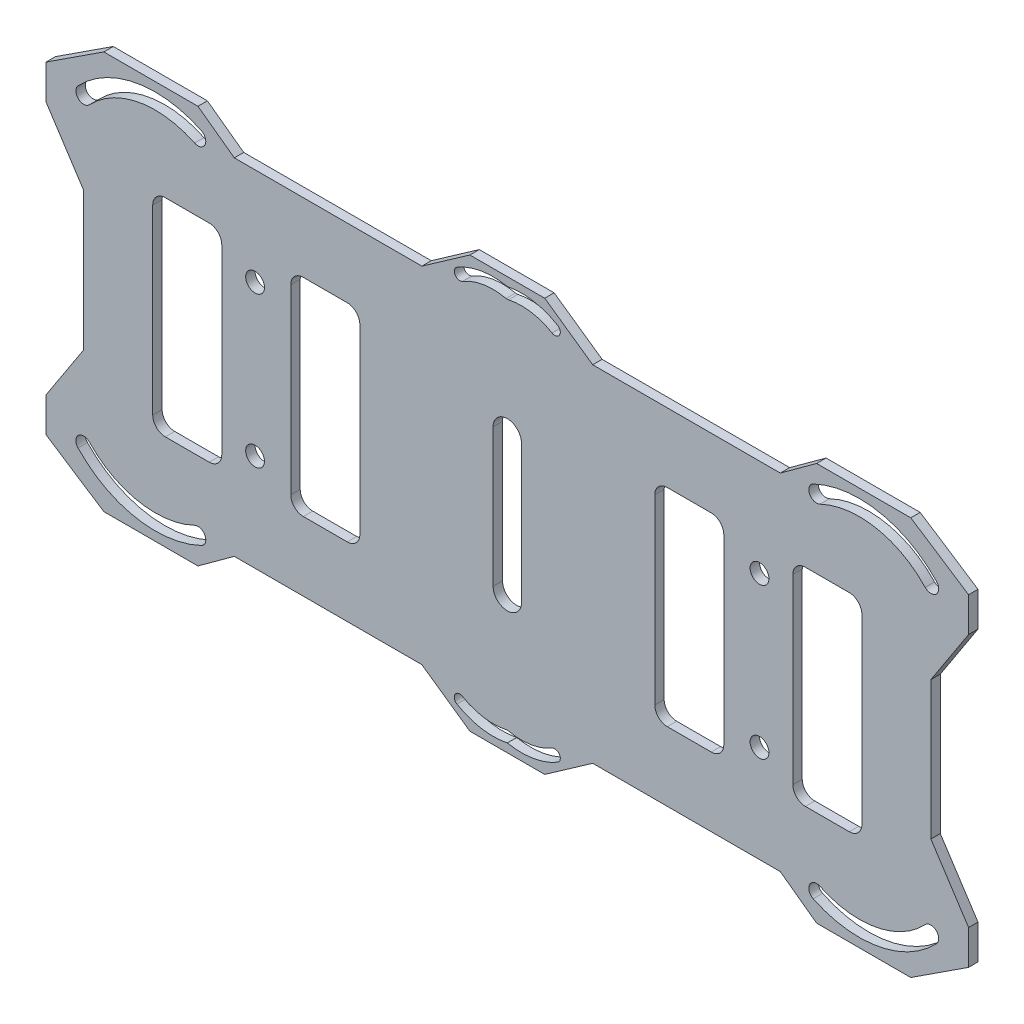
SolidWorks part; units mm, degrees
ref_plane "Piano frontale" through (0, 0, 0) normal (0, 0, 1) x (1, 0, 0)
ref_plane "Piano superiore" through (0, 0, 0) normal (0, 1, 0) x (1, 0, 0)
ref_plane "Piano destro" through (0, 0, 0) normal (1, 0, 0) x (0, 0, -1)
sketch "Schizzo1" plane through (0, 0, 0) normal (0, 0, 1) x (1, 0, 0)
  line L0 (-13.6152, -27.5) -> (-5.9645, -32.8595)
  line L1 (13.6152, -27.5) -> (43.5, -27.5)
  line L2 (-67.5, -11) -> (-67.5, 11)
  line L5 (-67.5, -27.5) -> (67.5, 27.5) construction
  line L6 (-67.5, 27.5) -> (67.5, -27.5) construction
  line L7 (55, 0) -> (-55, 0) construction
  line L8 (-54.5, -16.5) -> (-47.5, -16.5)
  line L9 (-56.5, -14.5) -> (-56.5, 14.5)
  line L11 (-45.5, -14.5) -> (-45.5, 14.5)
  line L12 (-56.5, -16.5) -> (-45.5, 16.5) construction
  line L13 (-56.5, 16.5) -> (-45.5, -16.5) construction
  line L14 (-67.5, -11) -> (-73.5081, -20.2143)
  line L15 (-32.5, -16.5) -> (-25.5, -16.5)
  line L16 (-34.5, -14.5) -> (-34.5, 14.5)
  line L18 (-23.5, -14.5) -> (-23.5, 14.5)
  line L19 (-34.5, -16.5) -> (-23.5, 16.5) construction
  line L20 (-34.5, 16.5) -> (-23.5, -16.5) construction
  line L21 (-73.5081, -20.2143) -> (-73.5081, -25.7143)
  line L22 (-73.5081, -25.7143) -> (-64.2938, -31.7224)
  line L23 (-64.2938, -31.7224) -> (-49.2938, -31.7224)
  line L24 (-49.2938, -31.7224) -> (-43.5, -27.5)
  line L25 (-5.9645, -32.8595) -> (5.9645, -32.8595)
  line L26 (0, -55) -> (0, 55) construction
  line L27 (13.6152, -27.5) -> (5.9645, -32.8595)
  line L29 (45.5, -14.5) -> (45.5, 14.5)
  line L30 (54.5, -16.5) -> (47.5, -16.5)
  line L31 (56.5, -14.5) -> (56.5, 14.5)
  line L33 (23.5, -14.5) -> (23.5, 14.5)
  line L34 (32.5, -16.5) -> (25.5, -16.5)
  line L35 (34.5, -14.5) -> (34.5, 14.5)
  line L36 (49.2938, -31.7224) -> (43.5, -27.5)
  line L37 (64.2938, -31.7224) -> (49.2938, -31.7224)
  line L38 (73.5081, -25.7143) -> (64.2938, -31.7224)
  line L39 (73.5081, -20.2143) -> (73.5081, -25.7143)
  line L40 (67.5, -11) -> (73.5081, -20.2143)
  line L41 (67.5, -11) -> (67.5, 11)
  line L42 (-13.6152, 27.5) -> (-43.5, 27.5)
  line L43 (43.5, -27.5) -> (13.6152, -27.5)
  line L44 (67.5, -11) -> (67.5, 11)
  line L45 (43.5, 27.5) -> (13.6152, 27.5)
  line L46 (-13.6152, -27.5) -> (-43.5, -27.5)
  line L47 (-67.5, -11) -> (-67.5, 11)
  line L48 (67.5, 11) -> (73.5081, 20.2143)
  line L49 (73.5081, 20.2143) -> (73.5081, 25.7143)
  line L50 (73.5081, 25.7143) -> (64.2938, 31.7224)
  line L51 (64.2938, 31.7224) -> (49.2938, 31.7224)
  line L52 (49.2938, 31.7224) -> (43.5, 27.5)
  line L53 (32.5, 16.5) -> (25.5, 16.5)
  line L54 (54.5, 16.5) -> (47.5, 16.5)
  line L55 (13.6152, 27.5) -> (5.9645, 32.8595)
  line L56 (-5.9645, 32.8595) -> (5.9645, 32.8595)
  line L57 (-49.2938, 31.7224) -> (-43.5, 27.5)
  line L58 (-64.2938, 31.7224) -> (-49.2938, 31.7224)
  line L59 (-73.5081, 25.7143) -> (-64.2938, 31.7224)
  line L60 (-73.5081, 20.2143) -> (-73.5081, 25.7143)
  line L61 (-32.5, 16.5) -> (-25.5, 16.5)
  line L62 (-67.5, 11) -> (-73.5081, 20.2143)
  line L63 (-54.5, 16.5) -> (-47.5, 16.5)
  line L64 (13.6152, 27.5) -> (43.5, 27.5)
  line L65 (-13.6152, 27.5) -> (-5.9645, 32.8595)
  line L66 (-67.5, 25.4461) -> (-67.5, 25.8768)
  line L67 (-67.5, 25.4461) -> (-67.5, 25.8768)
  line L68 (0, 11) -> (0, -11) construction
  line L69 (2.2614, 11) -> (2.2614, -11)
  line L70 (-2.2614, 11) -> (-2.2614, -11)
  arc A0 (-25.5, -16.5) -> (-23.5, -14.5) centre (-25.5, -14.5) ccw
  arc A1 (-32.5, -16.5) -> (-34.5, -14.5) centre (-32.5, -14.5) cw
  arc A6 (-47.5, -16.5) -> (-45.5, -14.5) centre (-47.5, -14.5) ccw
  arc A7 (-54.5, -16.5) -> (-56.5, -14.5) centre (-54.5, -14.5) cw
  arc A8 (-67.5, -24.1318) -> (-49.2938, -27.5) centre (-56.089, -13.341) ccw construction
  arc A9 (-68.4056, -24.9882) -> (-48.7545, -28.6237) centre (-56.089, -13.341) ccw
  arc A10 (-66.5944, -23.2754) -> (-49.8331, -26.3763) centre (-56.089, -13.341) ccw
  arc A11 (-66.5944, -23.2754) -> (-68.4056, -24.9882) centre (-67.5, -24.1318) ccw
  arc A12 (-48.7545, -28.6237) -> (-49.8331, -26.3763) centre (-49.2938, -27.5) ccw
  circle A13 centre (-40.1914, -12) radius 1.5
  circle A14 centre (40.1914, 12) radius 1.5
  arc A15 (-8.0181, -30.1482) -> (0.1871, -31.4567) centre (-2.2501, -20.359) ccw
  arc A16 (-7.1323, -28.6449) -> (-0.1871, -29.7524) centre (-2.2501, -20.359) ccw
  arc A17 (-7.1323, -28.6449) -> (-8.0181, -30.1482) centre (-7.5752, -29.3966) ccw
  arc A18 (0.1871, -29.7524) -> (-0.1871, -29.7524) centre (0, -30.6046) ccw
  circle A19 centre (40.1914, -12) radius 1.5
  arc A20 (8.0181, -30.1482) -> (-0.1871, -31.4567) centre (2.2501, -20.359) cw
  arc A21 (7.1323, -28.6449) -> (0.1871, -29.7524) centre (2.2501, -20.359) cw
  arc A22 (7.1323, -28.6449) -> (8.0181, -30.1482) centre (7.5752, -29.3966) cw
  arc A23 (-0.1871, -29.7524) -> (0.1871, -29.7524) centre (0, -30.6046) cw
  arc A25 (47.5, -16.5) -> (45.5, -14.5) centre (47.5, -14.5) cw
  arc A27 (54.5, -16.5) -> (56.5, -14.5) centre (54.5, -14.5) ccw
  arc A29 (25.5, -16.5) -> (23.5, -14.5) centre (25.5, -14.5) cw
  arc A30 (32.5, -16.5) -> (34.5, -14.5) centre (32.5, -14.5) ccw
  arc A32 (67.5, -24.1318) -> (49.2938, -27.5) centre (56.089, -13.341) cw construction
  arc A33 (68.4056, -24.9882) -> (48.7545, -28.6237) centre (56.089, -13.341) cw
  arc A34 (66.5944, -23.2754) -> (49.8331, -26.3763) centre (56.089, -13.341) cw
  arc A35 (66.5944, -23.2754) -> (68.4056, -24.9882) centre (67.5, -24.1318) cw
  arc A36 (48.7545, -28.6237) -> (49.8331, -26.3763) centre (49.2938, -27.5) cw
  arc A37 (-67.5, 24.1318) -> (-49.2938, 27.5) centre (-56.089, 13.341) cw construction
  arc A38 (-68.4056, 24.9882) -> (-48.7545, 28.6237) centre (-56.089, 13.341) cw
  arc A39 (-66.5944, 23.2754) -> (-49.8331, 26.3763) centre (-56.089, 13.341) cw
  arc A40 (-66.5944, 23.2754) -> (-68.4056, 24.9882) centre (-67.5, 24.1318) cw
  arc A41 (-48.7545, 28.6237) -> (-49.8331, 26.3763) centre (-49.2938, 27.5) cw
  arc A42 (67.5, 24.1318) -> (49.2938, 27.5) centre (56.089, 13.341) ccw construction
  arc A43 (68.4056, 24.9882) -> (48.7545, 28.6237) centre (56.089, 13.341) ccw
  arc A44 (66.5944, 23.2754) -> (49.8331, 26.3763) centre (56.089, 13.341) ccw
  arc A45 (66.5944, 23.2754) -> (68.4056, 24.9882) centre (67.5, 24.1318) ccw
  arc A46 (48.7545, 28.6237) -> (49.8331, 26.3763) centre (49.2938, 27.5) ccw
  arc A47 (2.2614, 11) -> (-2.2614, 11) centre (0, 11) ccw
  arc A48 (-2.2614, -11) -> (2.2614, -11) centre (0, -11) ccw
  arc A49 (32.5, 16.5) -> (34.5, 14.5) centre (32.5, 14.5) cw
  arc A50 (25.5, 16.5) -> (23.5, 14.5) centre (25.5, 14.5) ccw
  arc A51 (54.5, 16.5) -> (56.5, 14.5) centre (54.5, 14.5) cw
  arc A52 (47.5, 16.5) -> (45.5, 14.5) centre (47.5, 14.5) ccw
  arc A53 (-0.1871, 29.7524) -> (0.1871, 29.7524) centre (0, 30.6046) ccw
  arc A54 (7.1323, 28.6449) -> (8.0181, 30.1482) centre (7.5752, 29.3966) ccw
  arc A55 (7.1323, 28.6449) -> (0.1871, 29.7524) centre (2.2501, 20.359) ccw
  arc A56 (8.0181, 30.1482) -> (-0.1871, 31.4567) centre (2.2501, 20.359) ccw
  arc A57 (0.1871, 29.7524) -> (-0.1871, 29.7524) centre (0, 30.6046) cw
  arc A58 (-7.1323, 28.6449) -> (-8.0181, 30.1482) centre (-7.5752, 29.3966) cw
  arc A59 (-7.1323, 28.6449) -> (-0.1871, 29.7524) centre (-2.2501, 20.359) cw
  arc A60 (-8.0181, 30.1482) -> (0.1871, 31.4567) centre (-2.2501, 20.359) cw
  circle A61 centre (-40.1914, 12) radius 1.5
  arc A62 (-54.5, 16.5) -> (-56.5, 14.5) centre (-54.5, 14.5) ccw
  arc A63 (-47.5, 16.5) -> (-45.5, 14.5) centre (-47.5, 14.5) cw
  arc A64 (-32.5, 16.5) -> (-34.5, 14.5) centre (-32.5, 14.5) ccw
  arc A65 (-25.5, 16.5) -> (-23.5, 14.5) centre (-25.5, 14.5) cw
  point P0 (0, 0)
  point P6 (-51, 0)
  point P13 (-29, 0)
  point P29 (-58.946, 28.7841)
  point P51 (-58.946, -28.7841)
  point P66 (-3.902, -30.7178)
  point P72 (0, -32.8595)
  point P76 (3.902, -30.7178)
  point P89 (58.946, 28.7841)
  point P108 (58.946, -28.7841)
  point P166 (3.902, 30.7178)
  point P167 (0, 32.8595)
  point P168 (-3.902, 30.7178)
  point P176 (0, 0)
  dimension "D8" = 2
  dimension "D15" = 3
  dimension "D1" = 135
  dimension "D2" = 55
  dimension "D3" = 16.5
  dimension "D4" = 11
  dimension "D5" = 38.5
  dimension "D6" = 11
  dimension "D7" = 33
  dimension "D9" = 11
  dimension "D10" = 11
  dimension "D11" = 5.5
  dimension "D12" = 11
  dimension "D13" = 15
  dimension "D14" = 24
  dimension "D16" = 12
extrude "Estrusione-Estrusione1" add sketch "Schizzo1" along normal mid plane 1.5 contours L65 L42 L57 L58 L59 L60 L62 L2 L14 L21 L22 L23 L24 L46 L0 L25 L27 L1 L36 L37 L38 L39 L40 L41 L48 L49 L50 L51 L52 L45 L55 L56 A58 A60 A56 A54 A55 A53 A59 A38 A41 A39 A40 A33 A36 A34 A35
